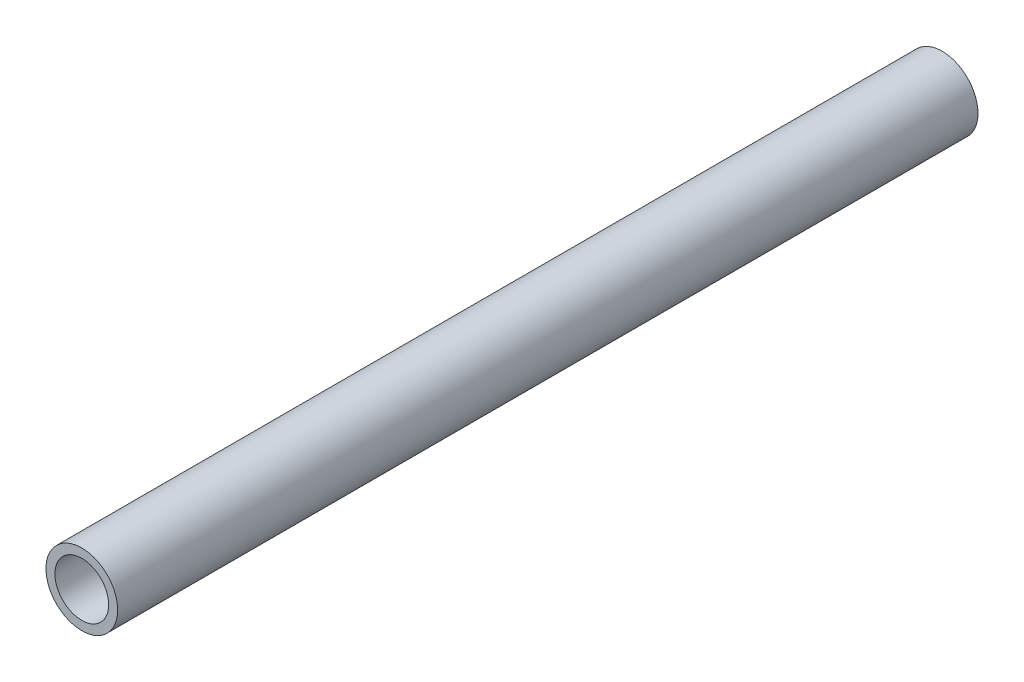
SolidWorks part; units mm, degrees
material "Zoltek Panex 33"
ref_plane "Front Plane" through (0, 0, 0) normal (0, 0, 1) x (1, 0, 0)
ref_plane "Top Plane" through (0, 0, 0) normal (0, 1, 0) x (1, 0, 0)
ref_plane "Right Plane" through (0, 0, 0) normal (1, 0, 0) x (0, 0, -1)
sketch "Sketch1" plane through (0, 0, 0) normal (0, 0, 1) x (1, 0, 0)
  circle A0 centre (0, 0) radius 6.35
  circle A1 centre (0, 0) radius 4.7625
  dimension "D1" = 12.7
  dimension "D2" = 9.525
extrude "Boss-Extrude1" add sketch "Sketch1" along normal mid plane 152.4
